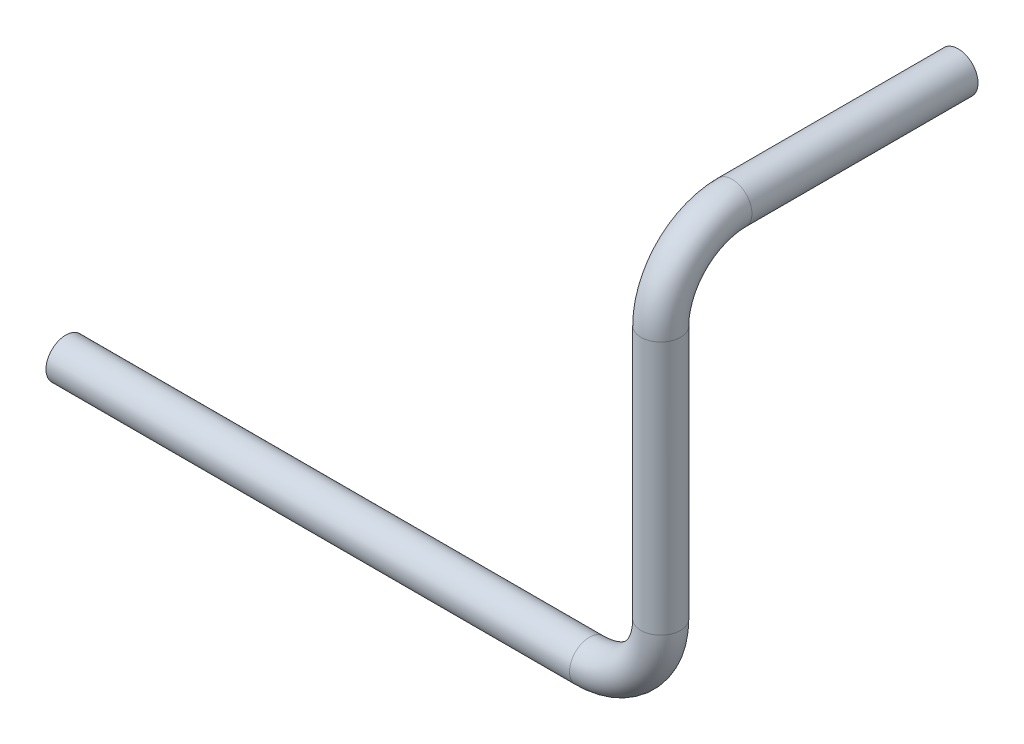
SolidWorks part; units mm, degrees
ref_plane "Ebene vorne" through (0, 0, 0) normal (0, 0, 1) x (1, 0, 0)
ref_plane "Ebene oben" through (0, 0, 0) normal (0, 1, 0) x (1, 0, 0)
ref_plane "Ebene rechts" through (0, 0, 0) normal (1, 0, 0) x (0, 0, -1)
sketch3d "3D-Skizze1"
  line L0 (0, 0, 0) -> (264, 0, 0)
  line L1 (300, 36, 0) -> (300, 164, 0)
  line L2 (300, 200, -36) -> (300, 200, -150)
  arc A0 (300, 164, 0) -> (300, 200, -36) centre (300, 164, -36) ccw
  arc A1 (264, 0, 0) -> (300, 36, 0) centre (264, 36, 0) ccw
  point P7 (300, 200, 0)
  point P8 (264, 164, -36)
  point P11 (300, 0, 0)
  point P12 (264, 36, 36)
sketch "Skizze1" plane through (0, 0, 0) normal (1, 0, 0) x (0, 0, -1)
  circle A0 centre (0, 0) radius 9
  dimension "D1" = 18
sweep "Austragung-Dünn1" add profiles "Skizze1" path "3D-Skizze1" parameters "D1"=1
equation "\"Länge\"= \"D1@3D-Skizze1\" + \"D2@3D-Skizze1\" + \"D3@3D-Skizze1\" + ( 2 * \"D4@3D-Skizze1\" )"
